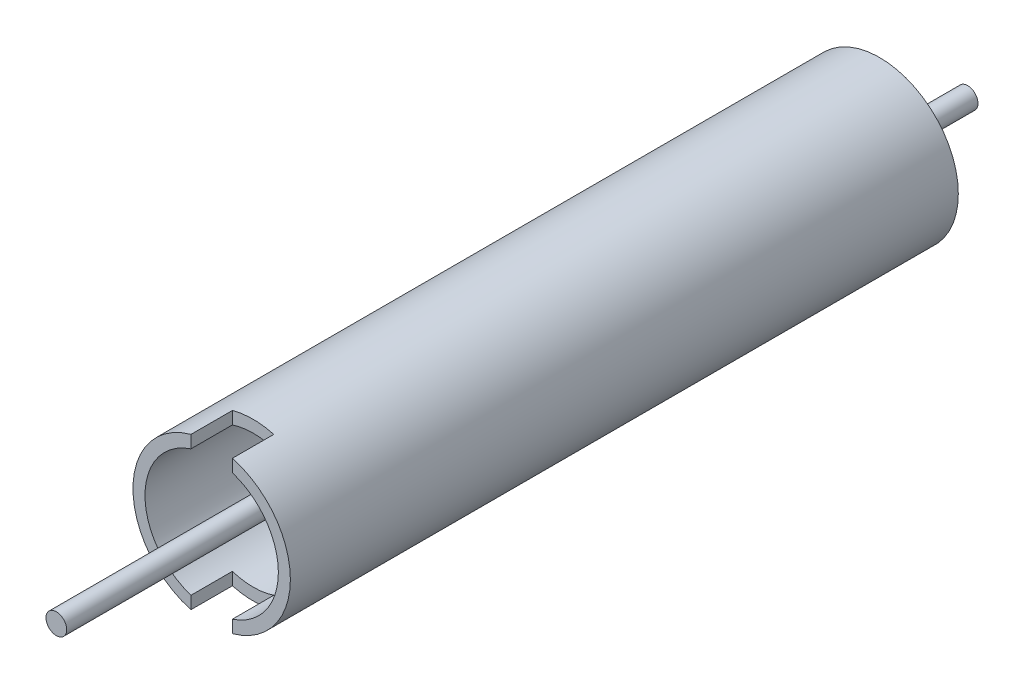
SolidWorks part; units mm, degrees
ref_plane "Front Plane" through (0, 0, 0) normal (0, 0, 1) x (1, 0, 0)
ref_plane "Top Plane" through (0, 0, 0) normal (0, 1, 0) x (1, 0, 0)
ref_plane "Right Plane" through (0, 0, 0) normal (1, 0, 0) x (0, 0, -1)
sketch "Sketch1" plane through (0, 0, 0) normal (0, 0, 1) x (1, 0, 0)
  circle A0 centre (0, 0) radius 3.175
extrude "Boss-Extrude1" add sketch "Sketch1" along normal mid plane 279.4 contours A0
sketch "Sketch2" plane through (0, 0, 0) normal (0, 0, 1) x (1, 0, 0)
  circle A0 centre (0, 0) radius 20.447
  circle A1 centre (0, 0) radius 24.13
  dimension "D1" = 40.894
  dimension "D2" = 48.26
extrude "Boss-Extrude2" add sketch "Sketch2" along normal blind 92.075 and the other way blind 112.7125
sketch "Sketch3" plane through (0, 0, 0) normal (0, 1, 0) x (1, 0, 0)
  line L0 (0, -92.075) -> (0, -79.375) construction
  line L1 (-24.13, -92.075) -> (24.13, -92.075) construction
  line L3 (6.35, -79.375) -> (-6.35, -79.375)
  line L4 (6.35, -79.375) -> (6.35, -92.075)
  line L5 (6.35, -92.075) -> (-6.35, -92.075)
  line L6 (-6.35, -79.375) -> (-6.35, -92.075)
  line L7 (6.35, -79.375) -> (-6.35, -92.075) construction
  line L8 (6.35, -92.075) -> (-6.35, -79.375) construction
  point P5 (0, -85.725)
  dimension "D1" = 12.7
  dimension "D2" = 12.7
extrude "Cut-Extrude1" cut sketch "Sketch3" along normal up to surface (3.8435 mm away) from surface
mirror "Mirror1" about plane through (0, 0, 0) normal (0, 1, 0) of "Cut-Extrude1"
